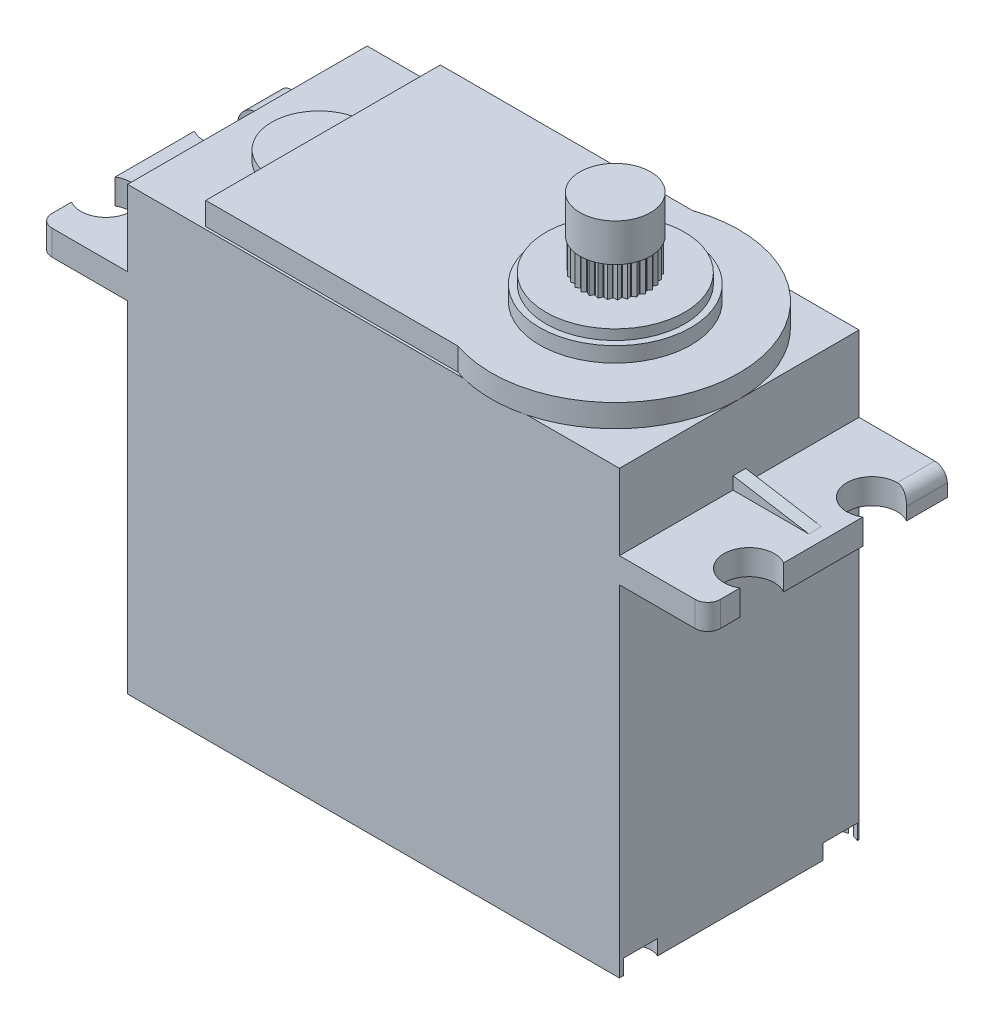
SolidWorks part; units mm, degrees
ref_plane "Front Plane" through (0, 0, 0) normal (0, 0, 1) x (1, 0, 0)
ref_plane "Top Plane" through (0, 0, 0) normal (0, 1, 0) x (1, 0, 0)
ref_plane "Right Plane" through (0, 0, 0) normal (1, 0, 0) x (0, 0, -1)
sketch "Sketch1" plane through (0, 0, 0) normal (0, 0, 1) x (1, 0, 0)
  line L1 (-23.6834, 8.2704) -> (15.3166, 8.2704)
  line L2 (-23.6834, 8.2704) -> (-23.6834, -26.7296)
  line L3 (-23.6834, -26.7296) -> (15.3166, -26.7296)
  line L4 (15.3166, 8.2704) -> (15.3166, -26.7296)
  dimension "D1" = 39
  dimension "D2" = 35
extrude "Boss-Extrude1" add sketch "Sketch1" along normal blind 19
sketch "Sketch2" plane through (0, 0, 19) normal (0, 0, 1) x (1, 0, 0)
  line L0 (15.3166, 8.2704) -> (15.3166, 2.2704) construction
  line L1 (15.3166, -26.7296) -> (15.3166, 8.2704) construction
  line L2 (-4.1834, 8.2704) -> (-4.1834, -3.6681) construction
  line L3 (15.3166, 2.2704) -> (22.3166, 2.2704)
  line L4 (15.3166, 2.2704) -> (15.3166, 0.2704)
  line L5 (15.3166, 0.2704) -> (22.3166, 0.2704)
  line L6 (22.3166, 2.2704) -> (22.3166, 0.2704)
  line L7 (15.3166, 8.2704) -> (-23.6834, 8.2704) construction
  line L8 (-30.6834, 2.2704) -> (-30.6834, 0.2704)
  line L9 (-23.6834, 2.2704) -> (-23.6834, 0.2704)
  line L10 (-23.6834, 0.2704) -> (-30.6834, 0.2704)
  line L11 (-23.6834, 2.2704) -> (-30.6834, 2.2704)
  dimension "D1" = 6
  dimension "D2" = 2
  dimension "D3" = 7
extrude "Boss-Extrude2" add sketch "Sketch2" against normal blind 19
ref_plane "Plane1" through (0, 0, 9.5) normal (0, 0, 1) x (1, 0, 0)
sketch "Sketch3" plane through (0, 0, 9.5) normal (0, 0, 1) x (1, 0, 0)
  line L0 (15.3336, 3.2723) -> (15.3336, 2.2723)
  line L1 (15.3336, 2.2723) -> (21.3336, 2.2723)
  line L2 (21.3336, 2.2723) -> (15.3336, 3.2723)
  line L3 (-23.6233, 8.3074) -> (15.2904, 8.3074) construction
  line L4 (-4.1665, 8.3074) -> (-4.1665, 2.2723) construction
  line L5 (-29.6665, 2.2723) -> (-23.6665, 3.2723)
  line L6 (-23.6665, 2.2723) -> (-29.6665, 2.2723)
  line L7 (-23.6665, 3.2723) -> (-23.6665, 2.2723)
  dimension "D1" = 1
  dimension "D2" = 6
extrude "Boss-Extrude3" add sketch "Sketch3" along normal mid plane 1
sketch "Sketch4" plane through (0, 2.2704, 0) normal (0, 1, 0) x (1, 0, 0)
  line L0 (21.3166, -14.7107) -> (21.3166, -19.7107) construction
  line L1 (21.3166, -4.967) -> (21.3166, 0) construction
  line L2 (22.3166, 0) -> (15.3166, 0) construction
  line L3 (15.3166, -14.7107) -> (21.3166, -14.7107) construction
  line L4 (15.3166, -19) -> (15.3166, 0) construction
  line L5 (15.3166, -4.967) -> (21.3166, -4.967) construction
  line L6 (-4.1834, 0) -> (-4.1834, -4.967) construction
  line L7 (15.3166, 0) -> (-23.6834, 0) construction
  circle A0 centre (21.3166, -14.7107) radius 2
  circle A1 centre (21.3166, -4.967) radius 2
  circle A2 centre (-29.6834, -14.7107) radius 2
  circle A3 centre (-29.6834, -4.967) radius 2
  dimension "D2" = 4
  dimension "D3" = 4
  dimension "D4" = 6
  dimension "D1" = 5
extrude "Cut-Extrude1" cut sketch "Sketch4" against normal blind 3
fillet "Fillet1" radius 1 4 edges at (-30.6834, 1.2704, 19) (-30.6834, 2.2704, 1.6175) (22.3166, 2.2704, 1.6175) (22.3166, 1.2704, 19)
sketch "Sketch5" plane through (0, 8.2704, 0) normal (0, 1, 0) x (1, 0, 0)
  line L0 (15.3166, -19) -> (-23.6834, -19) construction
  line L4 (-17.6834, -0.2) -> (-17.6834, -18.8)
  line L5 (-17.6834, -18.8) -> (2.3166, -18.8)
  line L6 (2.3166, -0.2) -> (-17.6834, -0.2)
  line L7 (-23.6834, -19) -> (-23.6834, 0) construction
  line L8 (15.3166, 0) -> (-23.6834, 0) construction
  arc A1 (2.3166, -0.2) -> (2.3166, -18.8) centre (5.49, -9.5) cw
  dimension "D1" = 0.2
  dimension "D2" = 0.2
  dimension "D3" = 6
  dimension "D4" = 20
extrude "Boss-Extrude4" add sketch "Sketch5" along normal blind 1.8
sketch "Sketch6" plane through (0, -26.7296, 0) normal (0, -1, 0) x (1, 0, 0)
  circle A0 centre (-22.6606, 17.3297) radius 1.5
  circle A1 centre (-22.6606, 1.4871) radius 1.5
  circle A2 centre (14.6705, 17.3297) radius 1.5
  circle A3 centre (14.6705, 1.4871) radius 1.5
  dimension "D1" = 3
extrude "Cut-Extrude2" cut sketch "Sketch6" against normal blind 1.2
sketch "Sketch7" plane through (0, 10.0704, 0) normal (0, 1, 0) x (1, 0, 0)
  line L0 (15.3166, -9.5) -> (5.49, -9.5) construction
  arc A0 (2.3166, -18.8) -> (2.3166, -0.2) centre (5.49, -9.5) ccw construction
  circle A1 centre (5.49, -9.5) radius 6
  dimension "D1" = 12
extrude "Boss-Extrude5" add sketch "Sketch7" along normal blind 1.2
sketch "Sketch8" plane through (0, 11.2704, 0) normal (0, 1, 0) x (1, 0, 0)
  circle A0 centre (5.49, -9.5) radius 5.5
  dimension "D1" = 11
extrude "Boss-Extrude6" add sketch "Sketch8" along normal blind 0.8
sketch "Sketch9" plane through (0, 8.2704, 0) normal (0, 1, 0) x (1, 0, 0)
  line L0 (-17.6834, -0.2) -> (-17.6834, -18.8) construction
  line L1 (-17.6834, -6.0659) -> (-17.6834, -13.5751)
  arc A0 (-17.6834, -6.0659) -> (-17.6834, -13.5751) centre (-17.6834, -9.8205) ccw
extrude "Boss-Extrude7" add sketch "Sketch9" along normal blind 0.8
sketch "Sketch10" plane through (0, 12.0704, 0) normal (0, 1, 0) x (1, 0, 0)
  circle A0 centre (5.49, -9.5) radius 2.5
  dimension "D1" = 5
extrude "Boss-Extrude8" add sketch "Sketch10" along normal blind 4
sketch "Sketch11" plane through (0, 16.0704, 0) normal (0, 1, 0) x (1, 0, 0)
  line L0 (5.5034, -6.8019) -> (5.2631, -7.0103)
  line L1 (5.2631, -7.0103) -> (5.7367, -7.0122)
  line L2 (5.7367, -7.0122) -> (5.5034, -6.8019)
  circle A0 centre (5.49, -9.5) radius 2.5 construction
extrude "Boss-Extrude9" add sketch "Sketch11" against normal blind 4
pattern_circular "CirPattern2" count 30 over 360 about axis through (5.49, 0, 9.5) along (0, 1, 0) of "Boss-Extrude9"
sketch "Sketch12" plane through (0, 16.0704, 0) normal (0, 1, 0) x (1, 0, 0)
  circle A0 centre (5.49, -9.5) radius 1.5
  dimension "D1" = 3
extrude "Cut-Extrude4" cut sketch "Sketch12" against normal blind 4
sketch "Sketch13" plane through (0, 16.0704, 0) normal (0, 1, 0) x (1, 0, 0)
  circle A0 centre (5.49, -9.5) radius 2.8
  dimension "D1" = 5.6
extrude "Boss-Extrude10" add sketch "Sketch13" along normal mid plane 3
sketch "Sketch14" plane through (0, 17.5704, 0) normal (0, 1, 0) x (1, 0, 0)
  circle A0 centre (5.49, -9.5) radius 10
  dimension "D1" = 20
